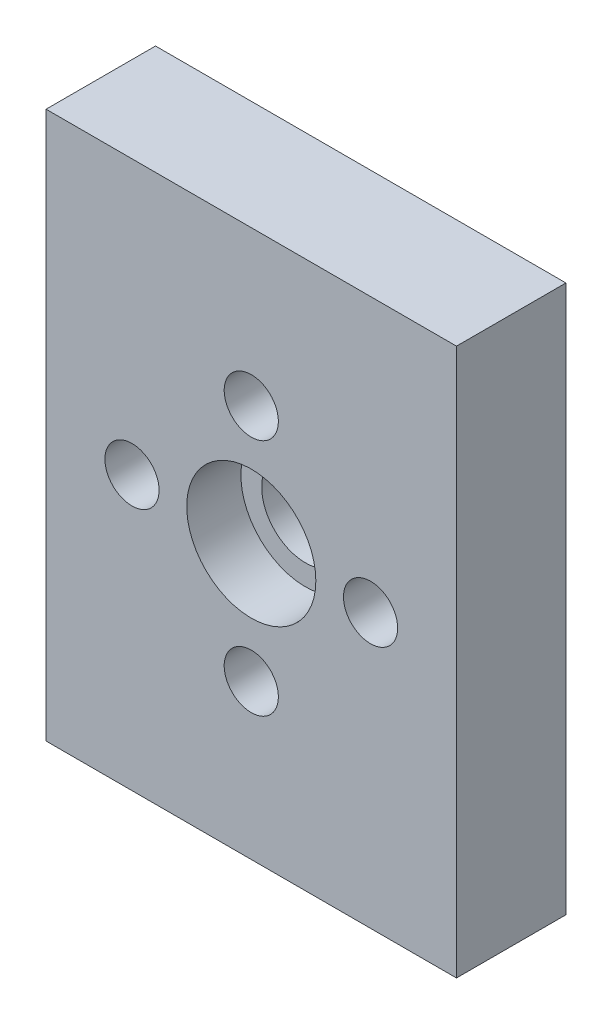
SolidWorks part; units mm, degrees
ref_plane "Front Plane" through (0, 0, 0) normal (0, 0, 1) x (1, 0, 0)
ref_plane "Top Plane" through (0, 0, 0) normal (0, 1, 0) x (1, 0, 0)
ref_plane "Right Plane" through (0, 0, 0) normal (1, 0, 0) x (0, 0, -1)
sketch "Sketch1" plane through (0, 0, 0) normal (0, 0, 1) x (1, 0, 0)
  line L1 (-9.525, -12.7) -> (9.525, -12.7)
  line L2 (-9.525, -12.7) -> (-9.525, 12.7)
  line L3 (-9.525, 12.7) -> (9.525, 12.7)
  line L4 (9.525, -12.7) -> (9.525, 12.7)
  line L5 (-9.525, -12.7) -> (9.525, 12.7) construction
  line L6 (-9.525, 12.7) -> (9.525, -12.7) construction
  point P0 (0, 0)
  dimension "D1" = 19.05
  dimension "D2" = 25.4
extrude "Boss-Extrude1" add sketch "Sketch1" along normal blind 5.08
sketch "Sketch2" plane through (0, 0, 5.08) normal (0, 0, 1) x (1, 0, 0)
  circle A0 centre (0, 0) radius 2.9972
  dimension "D1" = 5.9944
extrude "Cut-Extrude1" cut sketch "Sketch2" against normal blind 2.5146 contours A0
sketch "Sketch3" plane through (0, 0, 2.5654) normal (0, 0, 1) x (1, 0, 0)
  circle A0 centre (0, 0) radius 2.032
  dimension "D1" = 4.064
extrude "Cut-Extrude2" cut sketch "Sketch3" against normal through all
sketch "Sketch4" plane through (0, 0, 5.08) normal (0, 0, 1) x (1, 0, 0)
  circle A0 centre (0, 5.5372) radius 1.2573
  circle A1 centre (0, 0) radius 2.9972 construction
  circle A2 centre (5.5372, 0) radius 1.2573
  circle A3 centre (0, -5.5372) radius 1.2573
  circle A4 centre (-5.5372, 0) radius 1.2573
  point P14 (0, 0)
  dimension "D1" = 2.5146
  dimension "D2" = 5.5372
  dimension "D3" = 4
extrude "Cut-Extrude4" cut sketch "Sketch4" against normal through all
